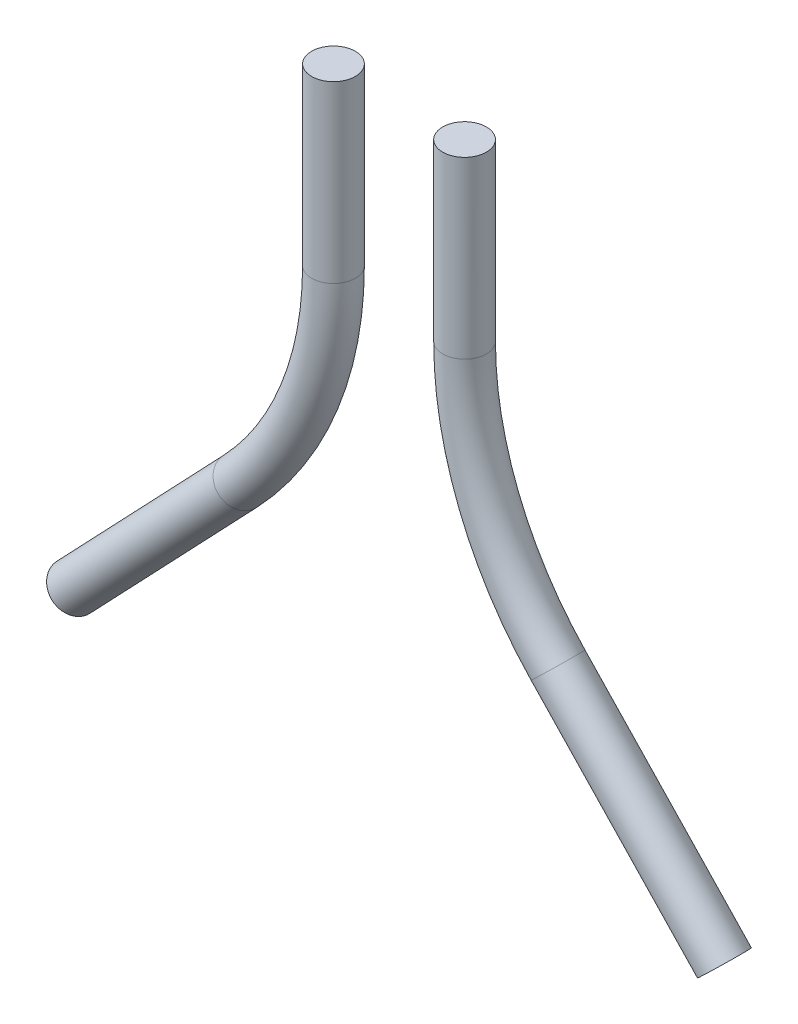
SolidWorks part; units mm, degrees
material "Chrome Stainless Steel"
ref_plane "Front Plane" through (0, 0, 0) normal (0, 0, 1) x (1, 0, 0)
ref_plane "Top Plane" through (0, 0, 0) normal (0, 1, 0) x (1, 0, 0)
ref_plane "Right Plane" through (0, 0, 0) normal (1, 0, 0) x (0, 0, -1)
sketch "Sketch1" plane through (0, 0, 0) normal (0, 0, 1) x (1, 0, 0)
  line L0 (2, -4.5) -> (3.9048, -6.5)
  line L1 (2.2, 0) -> (-2.2, 0) construction
  line L2 (1, 0) -> (1, -2)
  line L3 (0, -3.575) -> (0, 3.575) construction
  arc A1 (1, -2) -> (2, -4.5) centre (4.625, -2) ccw
  dimension "D1" = 4.5
  dimension "D2" = 2
  dimension "D3" = 1
  dimension "D4" = 2
  dimension "D5" = 6.5
sketch "Sketch2" plane through (0, 0, 0) normal (0, 1, 0) x (1, 0, 0)
  line L0 (-1.8657, 0) -> (1.8657, 0) construction
  circle A0 centre (0.75, 0) radius 0.25
  dimension "D1" = 0.5
sweep "Sweep1" add profiles "Sketch2" path "Sketch1"
mirror "Mirror3" about plane through (0, 0, 0) normal (1, 0, 0) of bodies 101
